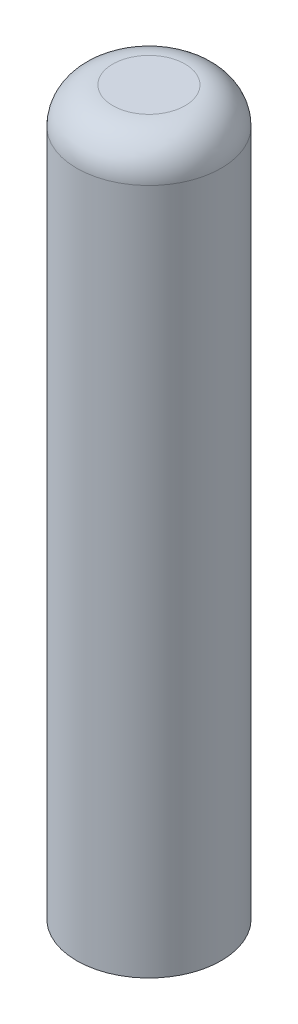
SolidWorks part; units mm, degrees
material "Chrome Stainless Steel"
ref_plane "Front Plane" through (0, 0, 0) normal (0, 0, 1) x (1, 0, 0)
ref_plane "Top Plane" through (0, 0, 0) normal (0, 1, 0) x (1, 0, 0)
ref_plane "Right Plane" through (0, 0, 0) normal (1, 0, 0) x (0, 0, -1)
sketch "Sketch3" plane through (0, 0, 0) normal (0, 1, 0) x (1, 0, 0)
  circle A0 centre (0, 0) radius 5.08
  dimension "D1" = 10.16
extrude "Boss-Extrude1" add sketch "Sketch3" along normal blind 50.8
cosmetic thread "Cosmetic Thread2" parameters "D1"=12.7, "D2"=5.08
fillet "Fillet2" radius 2.54 1 edges at (0, 50.8, 5.08)
